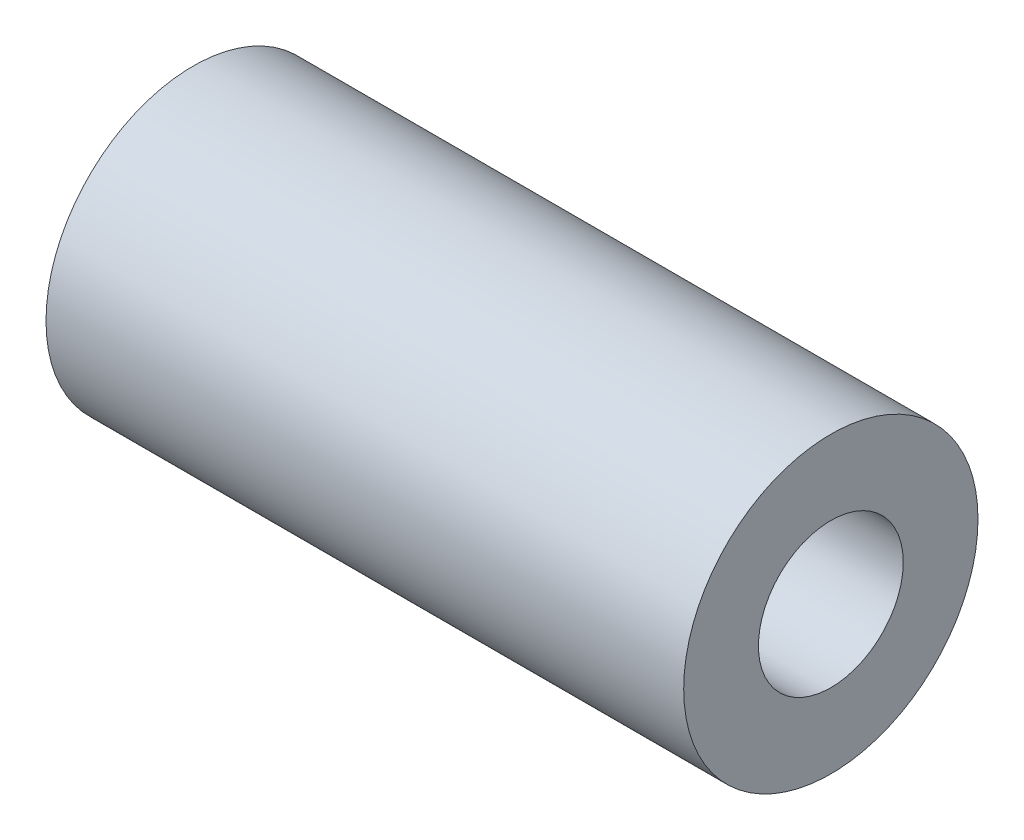
SolidWorks part; units mm, degrees
ref_plane "Front" through (0, 0, 0) normal (0, 0, 1) x (1, 0, 0)
ref_plane "Top" through (0, 0, 0) normal (0, 1, 0) x (1, 0, 0)
ref_plane "Right" through (0, 0, 0) normal (1, 0, 0) x (0, 0, -1)
sketch "Sketch1" plane through (0, 0, 0) normal (1, 0, 0) x (0, 0, -1)
  circle A0 centre (0, 0) radius 1.875
  circle A1 centre (0, 0) radius 3.81
  dimension "D1" = 3.75
  dimension "D2" = 7.62
extrude "Boss-Extrude1" add sketch "Sketch1" along normal blind 16.51
